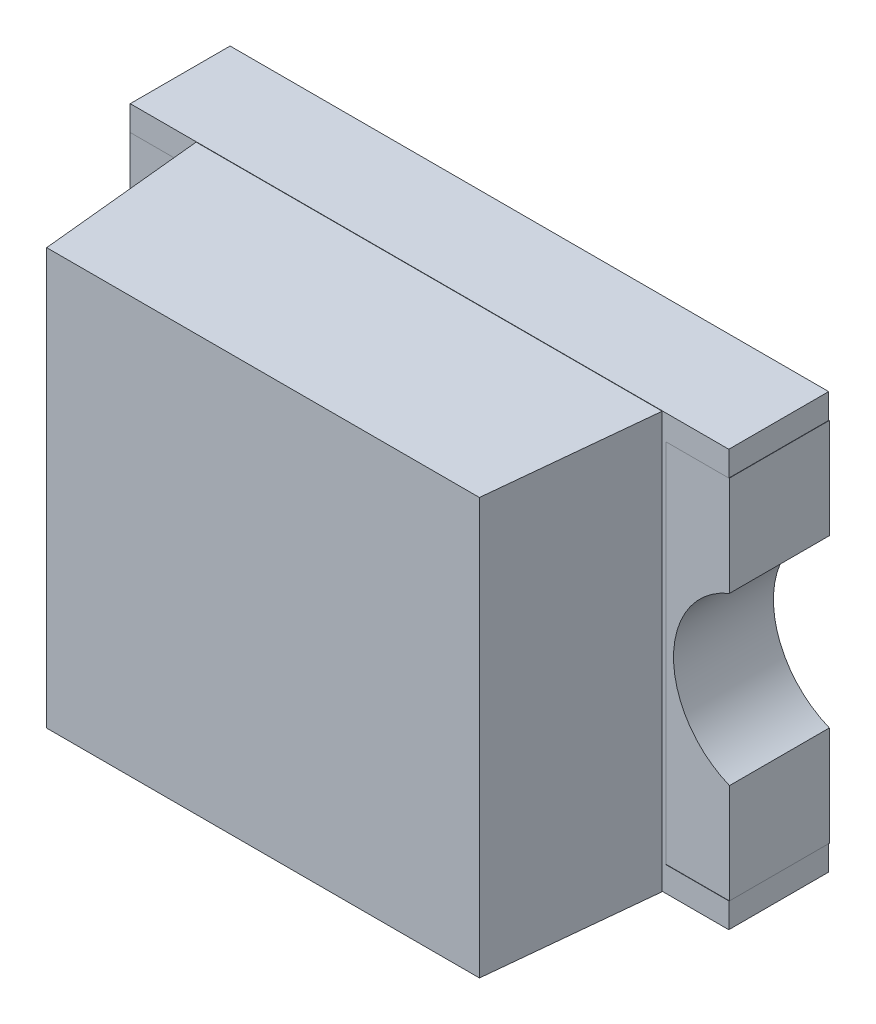
SolidWorks part; units mm, degrees
ref_plane "FRONT" through (0, 0, 0) normal (0, 0, 1) x (1, 0, 0)
ref_plane "TOP" through (0, 0, 0) normal (0, 1, 0) x (1, 0, 0)
ref_plane "RIGHT" through (0, 0, 0) normal (1, 0, 0) x (0, 0, -1)
sketch "Sketch1" plane through (0, 0, 0) normal (0, 0, 1) x (1, 0, 0)
  line L0 (-0.502, 0.55) -> (0, 0.55) construction
  line L1 (0, 0) -> (-0.4, 0)
  line L2 (0, 0) -> (0, 1.1)
  line L3 (0, 1.1) -> (-0.4, 1.1)
  line L4 (-0.4, 0) -> (-0.4, 0.3)
  line L5 (1, 0) -> (1.4, 0)
  line L6 (1, 0) -> (1, 1.1)
  line L7 (1, 1.1) -> (1.4, 1.1)
  line L8 (1.4, 0) -> (1.4, 0.3)
  line L9 (0, 0.55) -> (1, 0.55) construction
  line L10 (1, 0.55) -> (1.502, 0.55) construction
  line L11 (-0.4, 0.8) -> (-0.4, 1.1)
  line L12 (1.4, 0.8) -> (1.4, 1.1)
  arc A0 (-0.4, 0.8) -> (-0.4, 0.3) centre (-0.502, 0.55) cw
  arc A1 (1.4, 0.8) -> (1.4, 0.3) centre (1.502, 0.55) ccw
  dimension "D4" = 0.5
  dimension "D5" = 0.27
  dimension "D1" = 0.4
  dimension "D2" = 1
  dimension "D3" = 1.1
extrude "Extrude1" add sketch "Sketch1" along normal blind 0.3
sketch "Sketch2" plane through (0, 0, 0.3) normal (0, 0, 1) x (1, 0, 0)
  line L0 (-0.399, 1.1) -> (-0.399, 1.175)
  line L1 (0, 1.1) -> (-0.4, 1.1) construction
  line L2 (-0.399, 1.175) -> (1.399, 1.175)
  line L3 (1.399, 1.175) -> (1.399, 1.1)
  line L4 (1.4, 1.1) -> (1, 1.1) construction
  line L5 (1.399, 1.1) -> (1, 1.1)
  line L6 (1, 1.1) -> (1, 0)
  line L7 (1, 0) -> (1.399, 0)
  line L8 (1, 0) -> (1.4, 0) construction
  line L9 (1.399, 0) -> (1.399, -0.075)
  line L10 (1.399, -0.075) -> (-0.399, -0.075)
  line L11 (-0.399, -0.075) -> (-0.399, 0)
  line L12 (-0.399, 0) -> (0, 0)
  line L13 (0, 0) -> (0, 1.1)
  line L14 (0, 1.1) -> (-0.399, 1.1)
  line L15 (0, 0.55) -> (1, 0.55) construction
  line L16 (1, 0.55) -> (0.5, 1.175) construction
  line L17 (0.5, 1.175) -> (0.5, -0.075) construction
  line L18 (1.4, 0.8) -> (1.4, 1.1) construction
  point P24 (0.5, 0.55)
  dimension "D1" = 1.25
  dimension "D2" = 0.001
extrude "Extrude2" add sketch "Sketch2" against normal blind 0.3 from offset 0.001 separate body
sketch "Sketch3" plane through (0, -0.075, 0) normal (0, -1, 0) x (1, 0, 0)
  line L0 (-0.399, 0.301) -> (1.399, 0.301) construction
  line L7 (-0.399, 0.151) -> (1.399, 0.151) construction
  line L8 (-0.399, 0.001) -> (-0.399, 0.301) construction
  line L9 (1.399, 0.001) -> (1.399, 0.301) construction
  line L10 (0.5, 0.001) -> (0.5, 0.801) construction
  line L11 (-0.2, 0.302) -> (1.2, 0.302)
  line L12 (1.15, 0.801) -> (1.2, 0.302)
  line L13 (-0.15, 0.801) -> (1.15, 0.801)
  line L14 (-0.2, 0.302) -> (-0.15, 0.801)
  dimension "D1" = 0.199
  dimension "D2" = 0.249
  dimension "D3" = 0.899
  dimension "D4" = 0.001
  dimension "D5" = 0.5
extrude "Extrude3" add sketch "Sketch3" against normal up to surface (1.25 mm away) up to face at (0.5, 1.175, 0.151)
sketch "Sketch4" plane through (0, 0, 0.301) normal (0, 0, 1) x (1, 0, 0)
  line L0 (0.75, 0.65) -> (0.95, 0.45) construction
  line L1 (0.75, 0.65) -> (0.95, 0.65)
  line L2 (0.75, 0.65) -> (0.75, 0.45)
  line L3 (0.75, 0.45) -> (0.95, 0.45)
  line L4 (0.95, 0.65) -> (0.95, 0.45)
  line L5 (-0.232, 0.55) -> (0.85, 0.55) construction
  line L6 (-0.4, 1.1) -> (-0.4, 0.8) construction
  arc A0 (-0.4, 0.3) -> (-0.4, 0.8) centre (-0.502, 0.55) ccw construction
  point P4 (0.85, 0.55)
  dimension "D1" = 1.25
  dimension "D2" = 0.2
extrude "Extrude4" cut sketch "Sketch4" along normal blind 0.2
sketch "Sketch5" plane through (0, 0, 0.301) normal (0, 0, 1) x (1, 0, 0)
  line L0 (0.75, 0.65) -> (0.9499, 0.4501) construction
  line L1 (0.75, 0.65) -> (0.9499, 0.65)
  line L2 (0.75, 0.65) -> (0.75, 0.4501)
  line L3 (0.75, 0.4501) -> (0.9499, 0.4501)
  line L4 (0.9499, 0.65) -> (0.9499, 0.4501)
  line L6 (-0.4, 0.3) -> (-0.4, 0) construction
  line L7 (-0.232, 0.55) -> (0.85, 0.55) construction
  arc A0 (-0.4, 0.3) -> (-0.4, 0.8) centre (-0.502, 0.55) ccw construction
  point P4 (0.85, 0.55)
  point P5 (-0.4, 0.15)
  dimension "D1" = 1.25
  dimension "D2" = 0.1999
extrude "Extrude5" add sketch "Sketch5" along normal blind 0.199 from offset 0.0001 separate body
sketch "Sketch6" plane through (0, 0, 0.3) normal (0, 0, 1) x (1, 0, 0)
  line L0 (1.4, 1.1) -> (1, 1.1) construction
  line L1 (1.21, 1.1) -> (1, 1.1)
  line L2 (1.21, 1.1) -> (1.21, 0)
  line L3 (1.21, 0) -> (1, 0)
  line L4 (1, 1.1) -> (1, 0)
  line L5 (0, 1.1) -> (-0.4, 1.1) construction
  line L6 (-0.21, 1.1) -> (0, 1.1)
  line L7 (-0.21, 1.1) -> (-0.21, 0)
  line L8 (-0.21, 0) -> (0, 0)
  line L9 (0, 1.1) -> (0, 0)
  line L10 (0, 1.1) -> (1, 0) construction
  line L11 (0, 0) -> (1, 1.1) construction
  point P13 (0.5, 0.55)
  dimension "D1" = 0.21
  dimension "D2" = 1
extrude "Extrude6" add sketch "Sketch6" along normal up to surface (0.001 mm away) up to face at (0.5, 0.55, 0.301)
